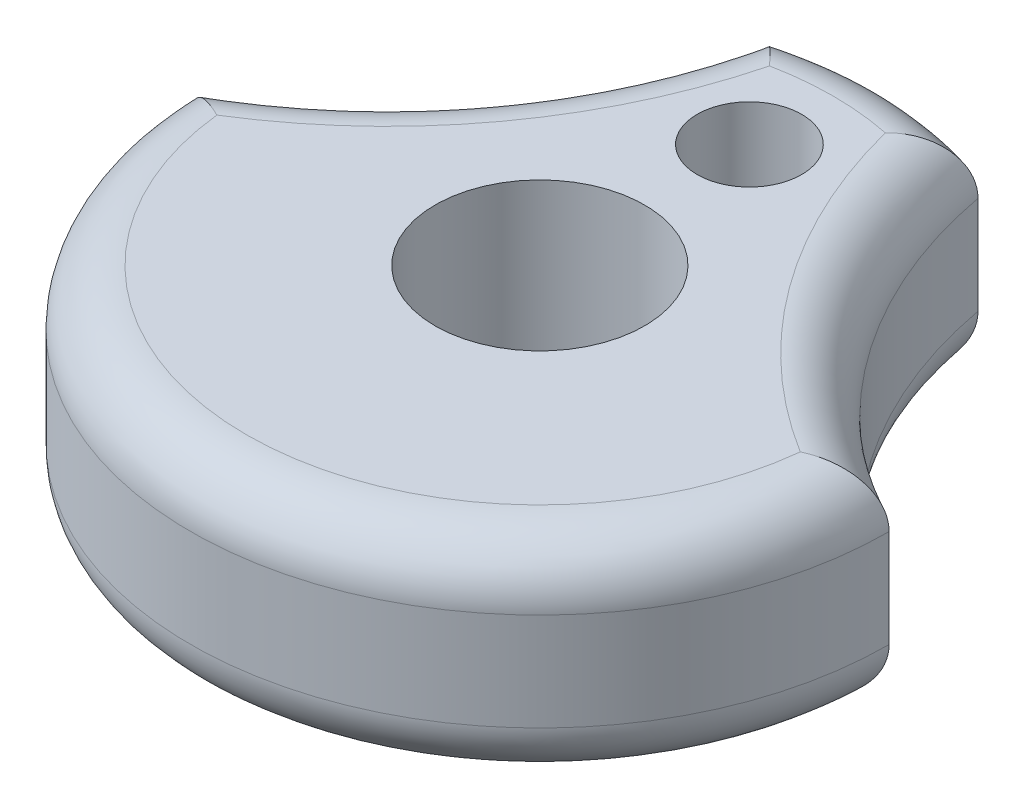
SolidWorks part; units mm, degrees
ref_plane "Front Plane" through (0, 0, 0) normal (0, 0, 1) x (1, 0, 0)
ref_plane "Top Plane" through (0, 0, 0) normal (0, 1, 0) x (1, 0, 0)
ref_plane "Right Plane" through (0, 0, 0) normal (1, 0, 0) x (0, 0, -1)
sketch "Sketch1" plane through (0, 0, 0) normal (0, 1, 0) x (1, 0, 0)
  line L0 (-6.25, 0) -> (6.25, 0) construction
  line L1 (0, -6.25) -> (0, 6.25) construction
  arc A6 (-6.25, 0) -> (6.25, 0) centre (0, 0) ccw
  arc A7 (-6.25, 0) -> (-1.88, 5.9605) centre (-10.2383, 7.5062) ccw
  arc A8 (6.25, 0) -> (1.88, 5.9605) centre (10.2383, 7.5062) cw
  arc A9 (1.88, 5.9605) -> (-1.88, 5.9605) centre (0, 0) ccw
  circle A10 centre (0, 0) radius 1.875
  circle A11 centre (0, 3.75) radius 0.935
  point P13 (0, 0)
  dimension "D1" = 1.88
  dimension "D2" = 12.5
  dimension "D3" = 8.5
  dimension "D4" = 6.25
  dimension "D5" = 3.75
  dimension "D6" = 3.75
  dimension "D7" = 1.87
extrude "Boss-Extrude1" add sketch "Sketch1" along normal blind 3.75
fillet "Fillet1" radius 1 4 edges at (3.3833, 3.75, -2.4804) (0, 3.75, -6.25) (-3.3833, 3.75, -2.4804) (0, 3.75, 6.25)
fillet "Fillet2" radius 1 4 edges at (-3.3833, 0, -2.4804) (0, 0, -6.25) (3.3833, 0, -2.4804) (0, 0, 6.25)
